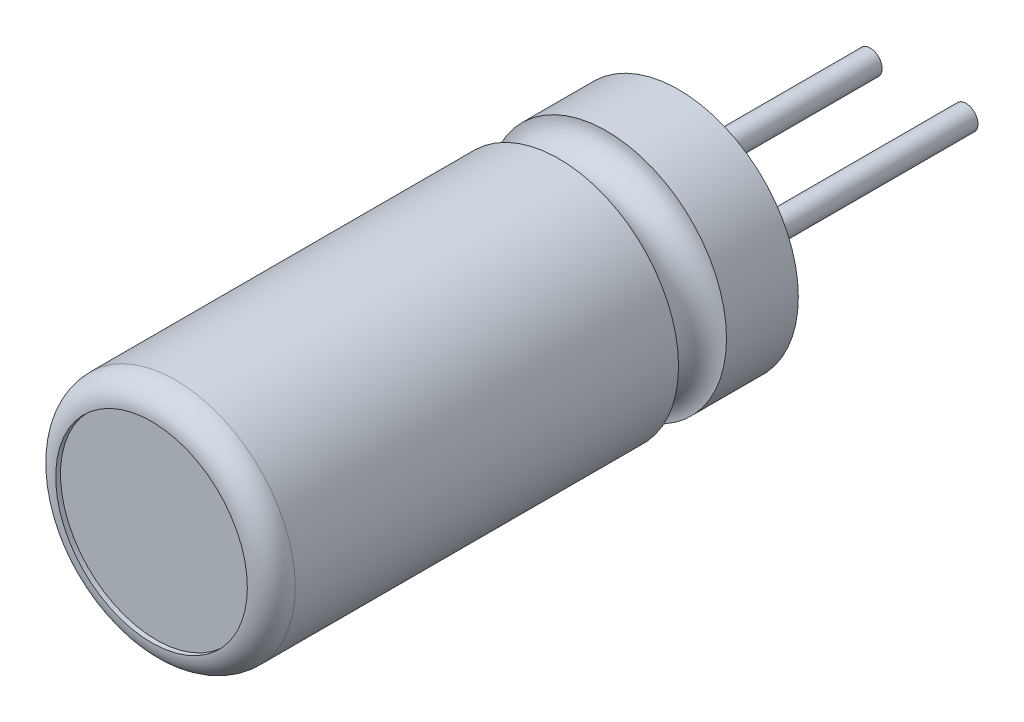
SolidWorks part; units mm, degrees
ref_plane "Front Plane" through (0, 0, 0) normal (0, 0, 1) x (1, 0, 0)
ref_plane "Top Plane" through (0, 0, 0) normal (0, 1, 0) x (1, 0, 0)
ref_plane "Right Plane" through (0, 0, 0) normal (1, 0, 0) x (0, 0, -1)
sketch "Sketch2" plane through (0, 0, 0) normal (1, 0, 0) x (0, 0, -1)
  line L0 (0, 0) -> (0, 2.5)
  line L1 (0, 2.5) -> (-1.5, 2.5)
  line L2 (-2.5, 2.5) -> (-10.5, 2.5)
  line L3 (-11, 2) -> (-11, 0)
  line L4 (-11, 0) -> (0, 0) construction
  line L5 (0, 0) -> (-11, 0)
  line L6 (0, 2.5) -> (0, -2.5) construction
  arc A0 (-1.5, 2.5) -> (-2.5, 2.5) centre (-2, 2.5) cw
  arc A1 (-10.5, 2.5) -> (-11, 2) centre (-10.5, 2) ccw
  point P11 (0, 0)
  dimension "D4" = 0.5
  dimension "D1" = 11
  dimension "D2" = 5
  dimension "D3" = 2
revolve "Base-Revolve" add sketch "Sketch2" angle 360 about L4
sketch "Sketch3" plane through (0, 0, 11) normal (0, 0, 1) x (1, 0, 0)
  circle A1 centre (0, 0) radius 2
  circle A2 centre (0, 0) radius 2
  dimension "D1" = 0
extrude "Cut-Extrude1" cut sketch "Sketch3" against normal blind 0.1
sketch "Sketch4" plane through (0, 0, 0) normal (0, 0, -1) x (-1, 0, 0)
  line L0 (1, 0) -> (-1, 0) construction
  circle A0 centre (1, 0) radius 0.25
  circle A1 centre (-1, 0) radius 0.25
  point P4 (0, 0)
  dimension "D2" = 0.5
  dimension "D1" = 2
extrude "Boss-Extrude1" add sketch "Sketch4" along normal blind 5
ref_plane "Board Plane" through (0, 0, -0.5) normal (0, 0, 1) x (1, 0, 0)
sketch "Component_Outline" plane through (0, 0, -0.5) normal (0, 0, 1) x (1, 0, 0)
  circle A0 centre (0, 0) radius 2.5
  circle A3 centre (-1, 0) radius 0.25 construction
  circle A4 centre (0, 0) radius 2.5 construction
  point P3 (-1, 0)
